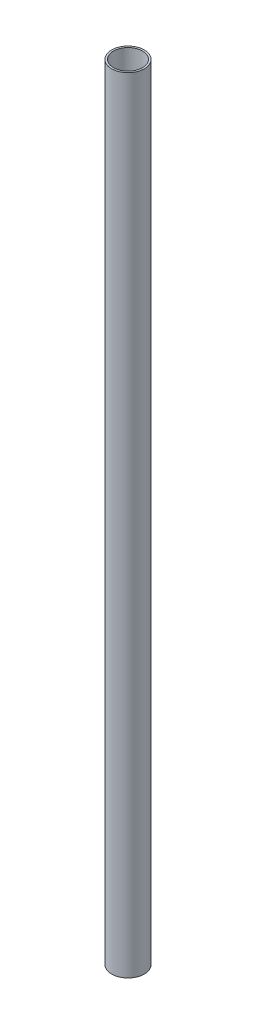
SolidWorks part; units mm, degrees
ref_plane "Front Plane" through (0, 0, 0) normal (0, 0, 1) x (1, 0, 0)
ref_plane "Top Plane" through (0, 0, 0) normal (0, 1, 0) x (1, 0, 0)
ref_plane "Right Plane" through (0, 0, 0) normal (1, 0, 0) x (0, 0, -1)
sketch "Sketch1" plane through (0, 0, 0) normal (0, 1, 0) x (1, 0, 0)
  circle A0 centre (0, 0) radius 6.35
  circle A1 centre (0, 0) radius 5.6388
  dimension "D1" = 12.7
  dimension "D2" = 11.2776
extrude "Boss-Extrude1" add sketch "Sketch1" along normal blind 304.8
